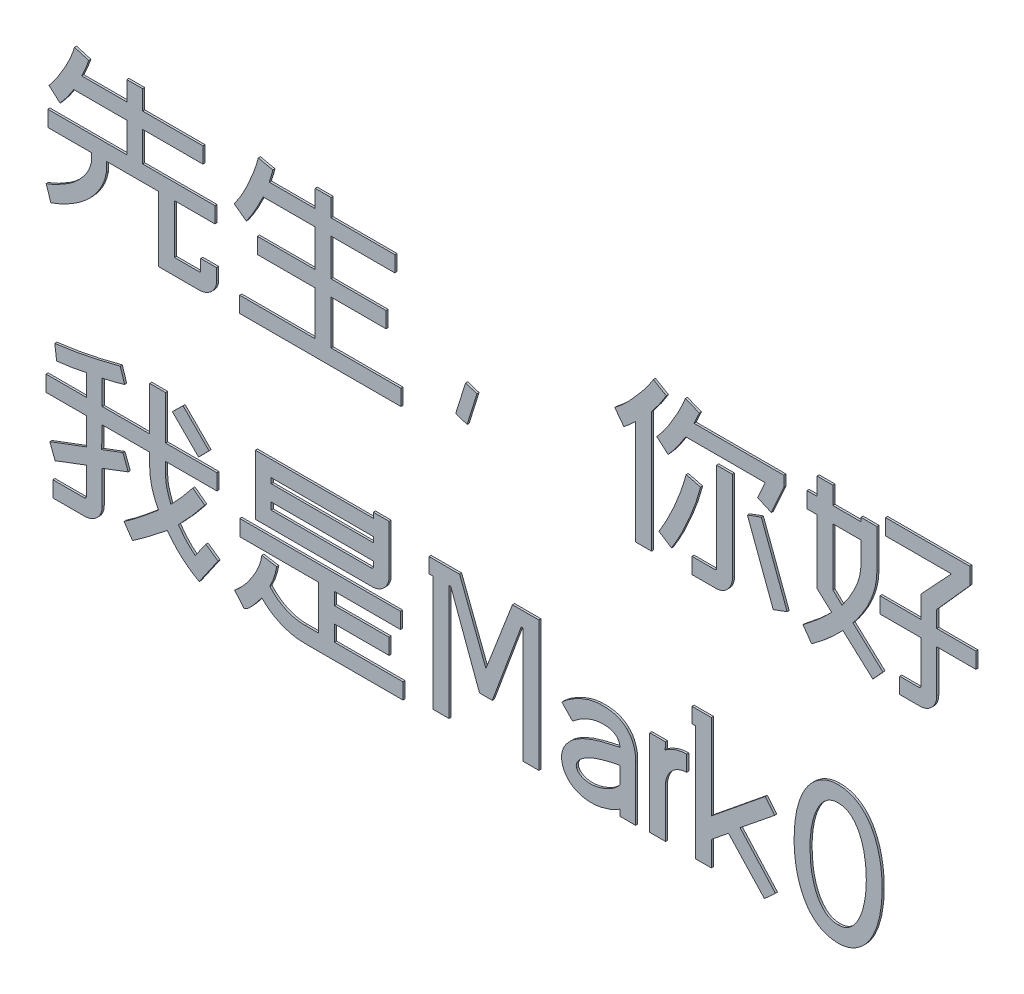
SolidWorks part; units mm, degrees
ref_plane "前视基准面" through (0, 0, 0) normal (0, 0, 1) x (1, 0, 0)
ref_plane "上视基准面" through (0, 0, 0) normal (0, 1, 0) x (1, 0, 0)
ref_plane "右视基准面" through (0, 0, 0) normal (1, 0, 0) x (0, 0, -1)
other "Configuration Table"
sketch "草图1" plane through (0, 0, 0) normal (0, 0, 1) x (1, 0, 0)
  line L0 (0, 17.4082) -> (0, -17.4082) construction
  line L1 (-26.7143, 0) -> (26.7143, 0) construction
  line L2 (25.5733, 12.1047) -> (25.5733, -12.1047) construction
  text T0 "先生，你好\r\n我是Mark0" font "站酷文艺体" height in points 15
  point P4 (0, 0)
  point P9 (0, 0)
  point P12 (25.5733, 0)
  dimension "D1" = 25.5733
extrude "凸台-拉伸1" add sketch "草图1" along normal blind 0.05
